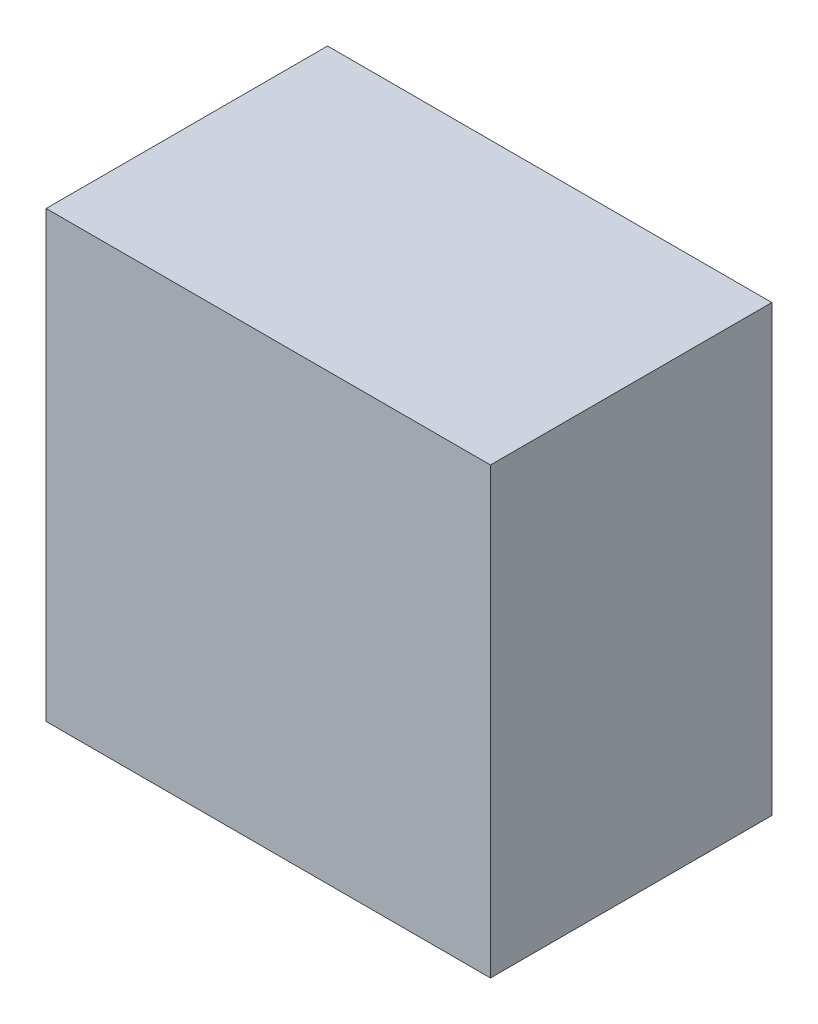
SolidWorks part; units mm, degrees
ref_plane "Front Plane" through (0, 0, 0) normal (0, 0, 1) x (1, 0, 0)
ref_plane "Top Plane" through (0, 0, 0) normal (0, 1, 0) x (1, 0, 0)
ref_plane "Right Plane" through (0, 0, 0) normal (1, 0, 0) x (0, 0, -1)
sketch "Sketch1" plane through (0, 0, 0) normal (0, 0, 1) x (1, 0, 0)
  line L1 (0, 0) -> (60, 0)
  line L2 (0, 0) -> (0, 60)
  line L3 (0, 60) -> (60, 60)
  line L4 (60, 0) -> (60, 60)
extrude "Boss-Extrude1" add sketch "Sketch1" along normal blind 38
